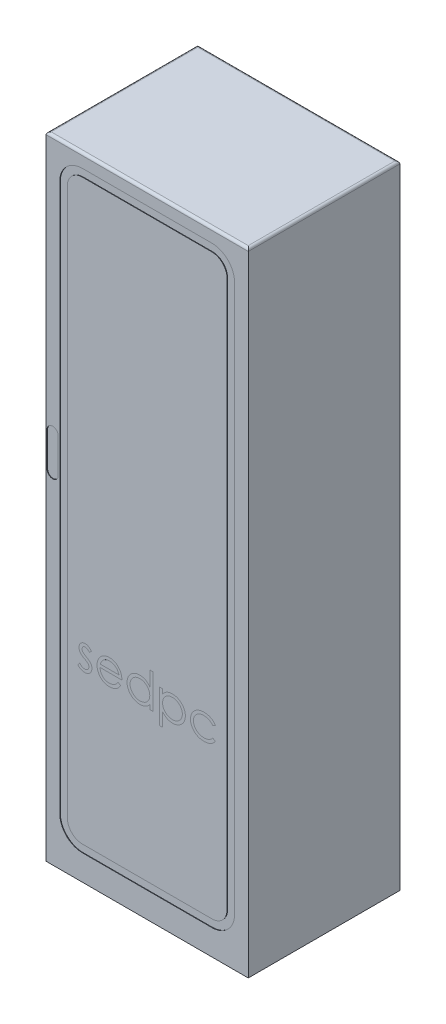
SolidWorks part; units mm, degrees
ref_plane "Alzado" through (0, 0, 0) normal (0, 0, 1) x (1, 0, 0)
ref_plane "Planta" through (0, 0, 0) normal (0, 1, 0) x (1, 0, 0)
ref_plane "Vista lateral" through (0, 0, 0) normal (1, 0, 0) x (0, 0, -1)
sketch "Croquis1" plane through (0, 0, 0) normal (0, 1, 0) x (1, 0, 0)
  line L1 (-400, 300) -> (400, 300)
  line L2 (-400, 300) -> (-400, -300)
  line L3 (-400, -300) -> (400, -300)
  line L4 (400, 300) -> (400, -300)
  line L5 (-400, 300) -> (400, -300) construction
  line L6 (-400, -300) -> (400, 300) construction
  point P0 (0, 0)
  dimension "D1" = 800
  dimension "D2" = 600
extrude "Saliente-Extruir1" add sketch "Croquis1" along normal blind 2500
sketch "Croquis2" plane through (0, 0, 300) normal (0, 0, 1) x (1, 0, 0)
  line L0 (-345.9954, 2356.5495) -> (-345.9954, 190.8498)
  line L1 (-255.9954, 2416.5495) -> (255.9954, 2416.5495)
  line L2 (-315.9954, 2356.5495) -> (-315.9954, 190.8498)
  line L3 (-255.9954, 130.8498) -> (255.9954, 130.8498)
  line L4 (315.9954, 2356.5495) -> (315.9954, 190.8498)
  line L5 (-315.9954, 2416.5495) -> (315.9954, 130.8498) construction
  line L6 (-315.9954, 130.8498) -> (315.9954, 2416.5495) construction
  line L7 (-255.9954, 100.8498) -> (255.9954, 100.8498)
  line L8 (345.9954, 2356.5495) -> (345.9954, 190.8498)
  line L9 (-255.9954, 2446.5495) -> (255.9954, 2446.5495)
  arc A0 (-315.9954, 190.8498) -> (-255.9954, 130.8498) centre (-255.9954, 190.8498) ccw
  arc A1 (255.9954, 130.8498) -> (315.9954, 190.8498) centre (255.9954, 190.8498) ccw
  arc A2 (255.9954, 2416.5495) -> (315.9954, 2356.5495) centre (255.9954, 2356.5495) cw
  arc A3 (-255.9954, 2416.5495) -> (-315.9954, 2356.5495) centre (-255.9954, 2356.5495) ccw
  arc A4 (-345.9954, 190.8498) -> (-255.9954, 100.8498) centre (-255.9954, 190.8498) ccw
  arc A5 (255.9954, 100.8498) -> (345.9954, 190.8498) centre (255.9954, 190.8498) ccw
  arc A6 (255.9954, 2446.5495) -> (345.9954, 2356.5495) centre (255.9954, 2356.5495) cw
  arc A7 (-255.9954, 2446.5495) -> (-345.9954, 2356.5495) centre (-255.9954, 2356.5495) ccw
  point P0 (0, 1273.6997)
  dimension "D1" = 60
  dimension "D2" = 30
extrude "Cortar-Extruir1" cut sketch "Croquis2" against normal blind 2
sketch "Croquis3" plane through (0, 0, 300) normal (0, 0, 1) x (1, 0, 0)
  line L0 (-374.0328, 1482.1163) -> (-374.0328, 1345.9345) construction
  line L1 (-352.0396, 1482.1163) -> (-352.0396, 1345.9345)
  line L2 (-396.0259, 1482.1163) -> (-396.0259, 1345.9345)
  arc A0 (-352.0396, 1482.1163) -> (-396.0259, 1482.1163) centre (-374.0328, 1482.1163) ccw
  arc A1 (-396.0259, 1345.9345) -> (-352.0396, 1345.9345) centre (-374.0328, 1345.9345) ccw
  point P2 (-374.0328, 1414.0254)
extrude "Cortar-Extruir2" cut sketch "Croquis3" against normal blind 2
sketch "Croquis4" plane through (0, 0, 300) normal (0, 0, 1) x (1, 0, 0)
  line L0 (-315.9954, 725.1537) -> (315.9954, 725.1537) construction
  line L1 (315.9954, 190.8498) -> (315.9954, 2356.5495) construction
  line L2 (-315.9954, 2356.5495) -> (-315.9954, 190.8498) construction
  text T0 "sedpc" font "Century Gothic" height in points 500
extrude "Cortar-Extruir3" cut sketch "Croquis4" against normal blind 0.001
fillet "Redondeo1" radius 10 4 edges at (0, 2500, -300) (-400, 2500, 0) (400, 2500, 0) (0, 2500, 300)
